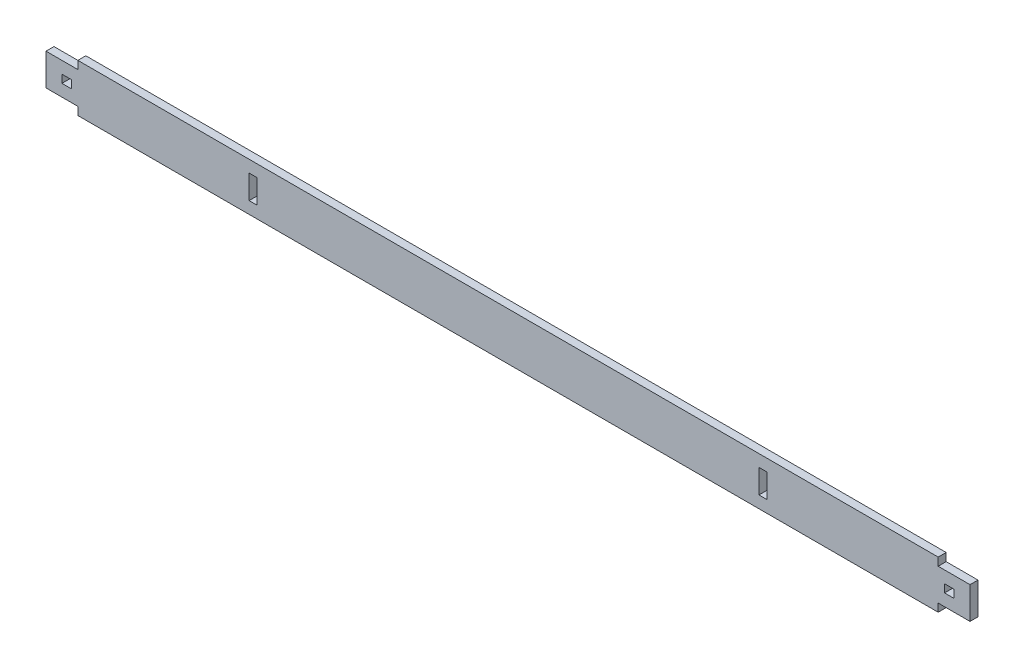
SolidWorks part; units mm, degrees
ref_plane "Front Plane" through (0, 0, 0) normal (0, 0, 1) x (1, 0, 0)
ref_plane "Top Plane" through (0, 0, 0) normal (0, 1, 0) x (1, 0, 0)
ref_plane "Right Plane" through (0, 0, 0) normal (1, 0, 0) x (0, 0, -1)
sketch "Sketch1" plane through (0, 0, 0) normal (0, 0, 1) x (1, 0, 0)
  line L1 (-342.9, -19.05) -> (342.9, -19.05)
  line L2 (-342.9, -19.05) -> (-342.9, 19.05)
  line L3 (-342.9, 19.05) -> (342.9, 19.05)
  line L4 (342.9, -19.05) -> (342.9, 19.05)
  line L5 (-342.9, -19.05) -> (342.9, 19.05) construction
  line L6 (-342.9, 19.05) -> (342.9, -19.05) construction
  point P0 (0, 0)
  dimension "D1" = 685.8
  dimension "D2" = 38.1
extrude "Boss-Extrude1" add sketch "Sketch1" along normal blind 6.35
sketch "Sketch2" plane through (0, 0, 6.35) normal (0, 0, 1) x (1, 0, 0)
  line L0 (-342.9, 19.05) -> (-342.9, -19.05) construction
  line L1 (-368.3, -12.7) -> (-317.5, -12.7)
  line L2 (-368.3, -12.7) -> (-368.3, 12.7)
  line L3 (-368.3, 12.7) -> (-317.5, 12.7)
  line L4 (-317.5, -12.7) -> (-317.5, 12.7)
  line L5 (-368.3, -12.7) -> (-317.5, 12.7) construction
  line L6 (-368.3, 12.7) -> (-317.5, -12.7) construction
  point P0 (-342.9, 0)
  dimension "D1" = 25.4
  dimension "D2" = 25.4
extrude "Boss-Extrude2" add sketch "Sketch2" against normal up to surface (6.35 mm away) up to face at (0, 0, 0)
sketch "Sketch3" plane through (0, 0, 6.35) normal (0, 0, 1) x (1, 0, 0)
  line L0 (-342.9, 19.05) -> (-342.9, 12.7) construction
  line L1 (-355.6, 3.175) -> (-347.98, 3.175)
  line L2 (-355.6, 3.175) -> (-355.6, -3.175)
  line L3 (-355.6, -3.175) -> (-347.98, -3.175)
  line L4 (-347.98, 3.175) -> (-347.98, -3.175)
  line L5 (-347.98, -12.7) -> (-347.98, -3.175) construction
  line L6 (-368.3, -12.7) -> (-342.9, -12.7) construction
  line L7 (-347.98, 3.175) -> (-347.98, 12.7) construction
  line L8 (-342.9, 12.7) -> (-368.3, 12.7) construction
  line L9 (-368.3, 12.7) -> (-368.3, -12.7) construction
  dimension "D1" = 5.08
  dimension "D2" = 6.35
  dimension "D3" = 12.7
extrude "Cut-Extrude1" cut sketch "Sketch3" against normal through all
mirror "Mirror1" about plane through (0, 0, 0) normal (1, 0, 0) of "Cut-Extrude1", "Boss-Extrude2"
sketch "Sketch4" plane through (0, 0, 6.35) normal (0, 0, 1) x (1, 0, 0)
  line L1 (-206.375, 9.525) -> (-200.025, 9.525)
  line L2 (-206.375, 9.525) -> (-206.375, -9.525)
  line L3 (-206.375, -9.525) -> (-200.025, -9.525)
  line L4 (-200.025, 9.525) -> (-200.025, -9.525)
  line L5 (-206.375, 9.525) -> (-200.025, -9.525) construction
  line L6 (-206.375, -9.525) -> (-200.025, 9.525) construction
  point P0 (-203.2, 0)
  dimension "D1" = 19.05
  dimension "D2" = 6.35
  dimension "D3" = 203.2
extrude "Cut-Extrude2" cut sketch "Sketch4" against normal through all
mirror "Mirror2" about plane through (0, 0, 0) normal (1, 0, 0) of "Cut-Extrude2"
